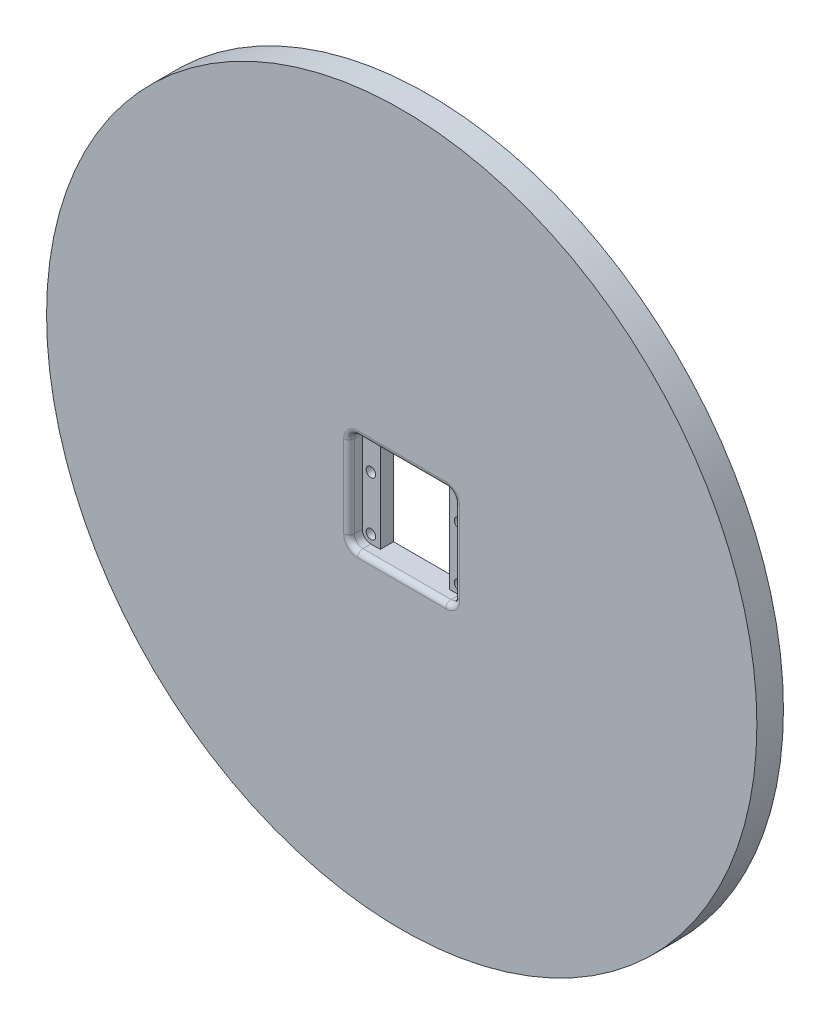
SolidWorks part; units mm, degrees
material "PET"
ref_plane "Front Plane" through (0, 0, 0) normal (0, 0, 1) x (1, 0, 0)
ref_plane "Top Plane" through (0, 0, 0) normal (0, 1, 0) x (1, 0, 0)
ref_plane "Right Plane" through (0, 0, 0) normal (1, 0, 0) x (0, 0, -1)
sketch "Sketch1" plane through (0, 0, 0) normal (0, 0, 1) x (1, 0, 0)
  circle A3 centre (0, 0) radius 84.9312
extrude "Boss-Extrude1" add sketch "Sketch1" along normal blind 6.35
sketch "Sketch2" plane through (0, 0, 6.35) normal (0, 0, 1) x (1, 0, 0)
  line L1 (10.541, 11.8999) -> (-10.541, 11.8999)
  line L2 (12.5984, 9.8425) -> (12.5984, -9.8425)
  line L3 (10.541, -11.8999) -> (-10.541, -11.8999)
  line L4 (-12.5984, 9.8425) -> (-12.5984, -9.8425)
  line L5 (12.5984, 11.8999) -> (-12.5984, -11.8999) construction
  line L6 (12.5984, -11.8999) -> (-12.5984, 11.8999) construction
  arc A0 (10.541, 11.8999) -> (12.5984, 9.8425) centre (10.541, 9.8425) cw
  arc A1 (-10.541, 11.8999) -> (-12.5984, 9.8425) centre (-10.541, 9.8425) ccw
  arc A2 (-10.541, -11.8999) -> (-12.5984, -9.8425) centre (-10.541, -9.8425) cw
  arc A3 (12.5984, -9.8425) -> (10.541, -11.8999) centre (10.541, -9.8425) cw
  point P0 (0, 0)
  dimension "D3" = 2.0574
  dimension "D1" = 25.1968
  dimension "D2" = 23.7998
extrude "Cut-Extrude2" cut sketch "Sketch2" against normal offset from surface (3.175 mm away) 3.175 contours A3 L2 A0 L1 A1 L4 A2 L3 up to face at (84.9312, 0, 0)
sketch "Sketch4" plane through (0, 0, 3.175) normal (0, 0, 1) x (1, 0, 0)
  line L0 (10.541, 11.8999) -> (-10.541, 11.8999) construction
  line L1 (10.541, -11.8999) -> (-10.541, -11.8999) construction
  line L2 (-12.5984, 9.8425) -> (-12.5984, -9.8425) construction
  line L3 (12.5984, 9.8425) -> (12.5984, -9.8425) construction
  line L4 (8.3058, -11.8999) -> (-8.3058, -11.8999)
  line L5 (8.3058, 11.8999) -> (-8.3058, 11.8999)
  line L13 (8.3058, -11.8999) -> (8.3058, 11.8999)
  line L15 (-8.3058, 11.8999) -> (-8.3058, -11.8999)
  circle A0 centre (10.541, -9.8425) radius 1.143
  circle A1 centre (-10.541, -9.8425) radius 1.143
  circle A2 centre (10.541, 2.9845) radius 1.143
  circle A3 centre (-10.541, 2.9845) radius 1.143
  dimension "D3" = 2.286
  dimension "D4" = 8.9154
  dimension "D1" = 4.2926
  dimension "D2" = 4.2926
extrude "Cut-Extrude3" cut sketch "Sketch4" against normal up to surface (3.175 mm away) up to face at (84.9312, 0, 0)
fillet "Fillet1" radius 1.27 8 edges at (11.9958, -11.2973, 6.35) (12.5984, 0, 6.35) (11.9958, 11.2973, 6.35) (0, 11.8999, 6.35) (-11.9958, 11.2973, 6.35) (-12.5984, 0, 6.35) (-11.9958, -11.2973, 6.35) (0, -11.8999, 6.35)
sketch "Sketch5" plane through (0, 0, 6.35) normal (0, 0, 1) x (1, 0, 0)
  line L0 (0, 0) -> (0, -84.9312) construction
  circle A0 centre (0, 0) radius 84.9312 construction
  circle A1 centre (0, 0) radius 84.9312 construction
  circle A2 centre (0, 0) radius 81.6292 construction
  circle A3 centre (0, -79.9782) radius 1.651
  circle A4 centre (0, 0) radius 79.9782 construction
  circle A5 centre (-79.9783, 0) radius 1.651
  circle A6 centre (0, 79.9782) radius 1.651
  circle A7 centre (79.9782, 0) radius 1.651
  point P18 (0, 0)
  dimension "D2" = 3.302
  dimension "D1" = 3.302
  dimension "D3" = 4
extrude "Cut-Extrude4" [suppressed] cut sketch "Sketch5" against normal up to surface (6.35 mm away)
